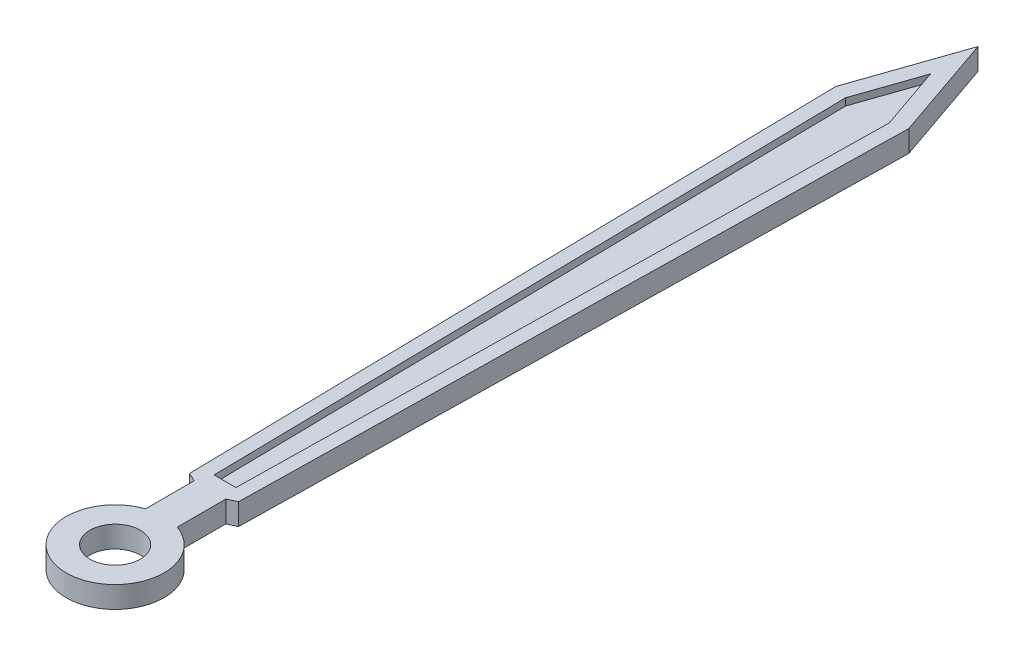
SolidWorks part; units mm, degrees
ref_plane "Front Plane" through (0, 0, 0) normal (0, 0, 1) x (1, 0, 0)
ref_plane "Top Plane" through (0, 0, 0) normal (0, 1, 0) x (1, 0, 0)
ref_plane "Right Plane" through (0, 0, 0) normal (1, 0, 0) x (0, 0, -1)
sketch "Sketch1" plane through (0, 0, 0) normal (0, 1, 0) x (1, 0, 0)
  line L0 (-0.2201, 1.3196) -> (-0.2201, 0.6434)
  line L1 (-0.5072, 10.5304) -> (0, 12)
  line L2 (0, 12) -> (0.5072, 10.5304)
  line L3 (0.2201, 0.6434) -> (0.2201, 1.3196)
  line L4 (0.5072, 10.5304) -> (0.3407, 1.3753)
  line L5 (0.3407, 1.3753) -> (0.2201, 1.3196)
  line L6 (-0.3407, 1.3753) -> (-0.2201, 1.3196)
  line L7 (-0.5072, 10.5304) -> (-0.3407, 1.3753)
  arc A2 (0.2201, 0.6434) -> (-0.2201, 0.6434) centre (0, 0) cw
extrude "Boss-Extrude1" add sketch "Sketch1" along normal blind 0.3
sketch "Sketch2" plane through (0, 0.3, 0) normal (0, 1, 0) x (1, 0, 0)
  circle A0 centre (0, 0) radius 0.35
extrude "Cut-Extrude1" cut sketch "Sketch2" against normal blind 0.3
sketch "Sketch3" plane through (0, 0.3, 0) normal (0, 1, 0) x (1, 0, 0)
  line L0 (0, 11.3409) -> (0.3039, 10.4603)
  line L1 (0.3039, 10.4603) -> (0.1519, 1.5278)
  line L2 (0.1519, 1.5278) -> (-0.1519, 1.5278)
  line L4 (-0.3039, 10.4603) -> (-0.1519, 1.5278)
  line L5 (0, 11.3409) -> (-0.3039, 10.4603)
extrude "Cut-Extrude2" cut sketch "Sketch3" against normal blind 0.1
